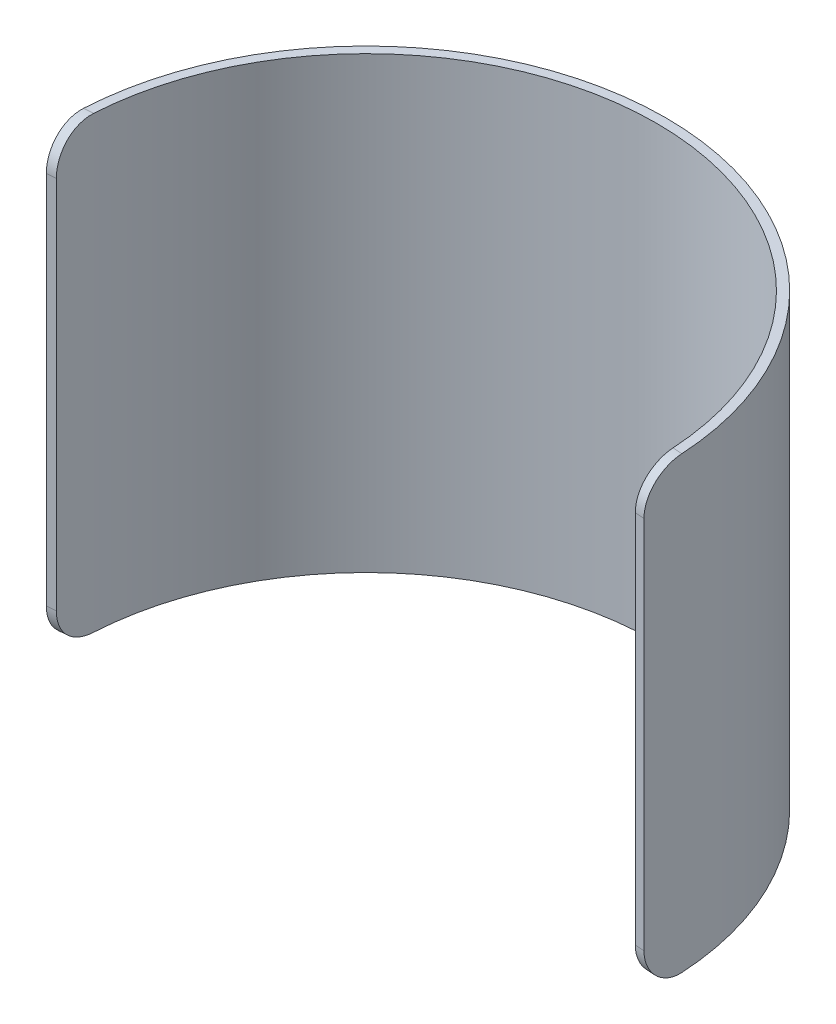
SolidWorks part; units mm, degrees
ref_plane "Front Plane" through (0, 0, 0) normal (0, 0, 1) x (1, 0, 0)
ref_plane "Top Plane" through (0, 0, 0) normal (0, 1, 0) x (1, 0, 0)
ref_plane "Right Plane" through (0, 0, 0) normal (1, 0, 0) x (0, 0, -1)
sketch "Sketch1" plane through (0, 0, 0) normal (0, 1, 0) x (1, 0, 0)
  circle A0 centre (0, 0) radius 98.425
  circle A1 centre (0, 0) radius 101.6
  dimension "D1" = 203.2
  dimension "D2" = 196.85
extrude "Boss-Extrude1" add sketch "Sketch1" along normal blind 152.4
sketch "Sketch2" plane through (0, 0, 0) normal (0, 1, 0) x (1, 0, 0)
  line L0 (0, 0) -> (-101.3525, -7.0873)
  line L1 (0, 0) -> (101.3525, -7.0873)
  line L2 (0, 0) -> (0, 101.6) construction
  circle A0 centre (0, 0) radius 101.6 construction
  circle A1 centre (0, 0) radius 101.6
  circle A2 centre (0, 0) radius 98.425 construction
  circle A3 centre (0, 0) radius 98.425
  dimension "D1" = 94
extrude "Cut-Extrude1" cut sketch "Sketch2" along normal blind 152.4 contours A3 L0 A1 L1
fillet "Fillet1" radius 12.7 4 edges at (99.7689, 0, 6.9765) (99.7689, 152.4, 6.9765) (-99.7689, 0, 6.9765) (-99.7689, 152.4, 6.9765)
